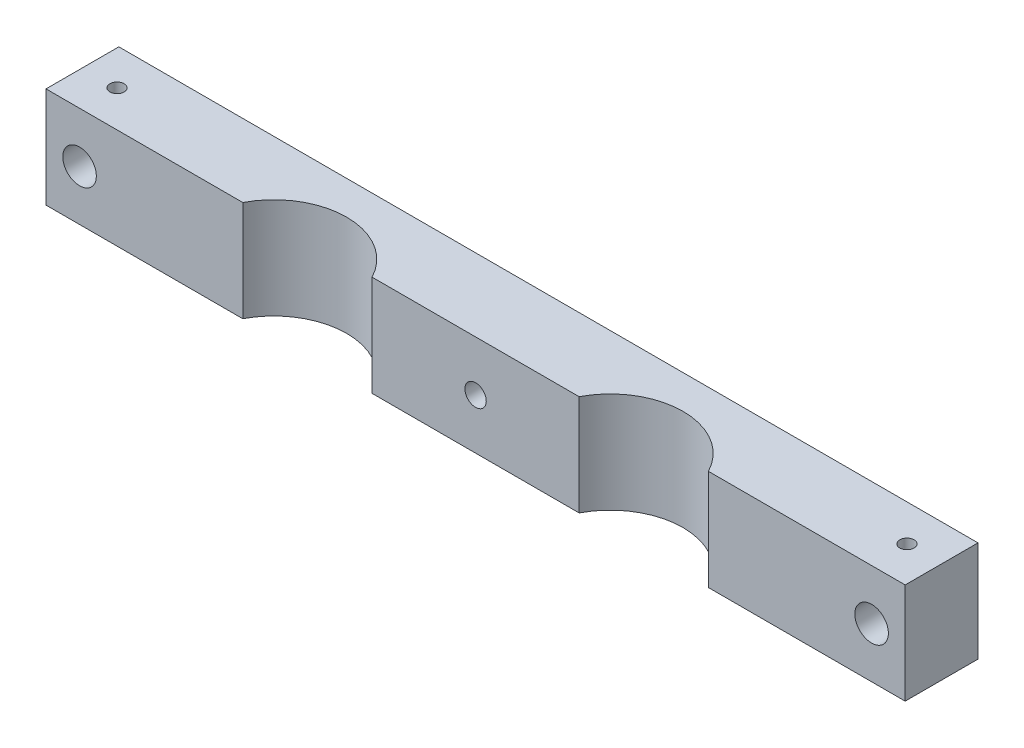
SolidWorks part; units mm, degrees
ref_plane "Front Plane" through (0, 0, 0) normal (0, 0, 1) x (1, 0, 0)
ref_plane "Top Plane" through (0, 0, 0) normal (0, 1, 0) x (1, 0, 0)
ref_plane "Right Plane" through (0, 0, 0) normal (1, 0, 0) x (0, 0, -1)
sketch "Sketch1" plane through (0, 0, 0) normal (0, 1, 0) x (1, 0, 0)
  line L0 (-19.5907, 0) -> (19.5907, 0)
  line L1 (-44.049, 0) -> (44.049, 0) construction
  line L2 (0, 0) -> (0, 13.7795) construction
  line L3 (-81.28, 13.7795) -> (81.28, 13.7795)
  line L4 (81.28, 0) -> (81.28, 13.7795)
  line L5 (44.049, 0) -> (81.28, 0)
  line L6 (-44.049, 0) -> (-81.28, 0)
  line L7 (-81.28, 0) -> (-81.28, 13.7795)
  arc A0 (-19.5907, 0) -> (-44.049, 0) centre (-31.8198, -6.35) ccw
  arc A1 (44.049, 0) -> (19.5907, 0) centre (31.8198, -6.35) ccw
  point P8 (-31.8198, 7.4295)
  dimension "D2" = 13.7795
  dimension "D1" = 162.56
  dimension "D3" = 6.35
  dimension "D4" = 63.6397
  dimension "D5" = 6.35
extrude "Boss-Extrude1" add sketch "Sketch1" along normal blind 19.05
hole_wizard "1/4 (0.25) Diameter Hole1" positions "Sketch3" profile "Sketch2" hole size "1/4" standard "ANSI Inch" end condition through all
sketch "Sketch3" plane through (0, 0, 0) normal (0, 0, 1) x (1, 0, 0)
  line L3 (-44.049, 0) -> (-81.28, 0) construction
  point P0 (-74.93, 9.525)
  dimension "D1" = 74.93
  dimension "D3" = 9.525
sketch "Sketch2" plane through (-74.93, 9.525, 0) normal (1, 0, 0) x (0, -1, 0)
  line L0 (0, 0) -> (0, 13.7795)
  line L1 (0, 13.7795) -> (3.175, 13.7795)
  line L2 (3.175, 13.7795) -> (3.175, 0)
  line L5 (3.175, 0) -> (0, 0)
  line L11 (0, -6.35) -> (0, 107.95) construction
  dimension "Thru Hole Dia." = 6.35
  dimension "Thru Hole Depth" = 13.7795
hole_wizard "#6-32 Tapped Hole1" positions "Sketch5" profile "Sketch4" tap size "#6-32" standard "ANSI Inch"
sketch "Sketch5" plane through (0, 19.05, 0) normal (0, 1, 0) x (1, 0, 0)
  line L0 (-81.28, 0) -> (-81.28, 13.7795) construction
  line L1 (-44.049, 0) -> (-81.28, 0) construction
  point P0 (-74.7293, 6.8897)
  dimension "D1" = 6.5507
  dimension "D2" = 6.8897
sketch "Sketch4" plane through (-74.7293, 19.05, -6.8897) normal (1, 0, 0) x (0, 0, 1)
  line L0 (0, 0) -> (0, 19.05)
  line L1 (0, 19.05) -> (1.3525, 19.05)
  line L2 (1.3525, 19.05) -> (1.3525, 0)
  line L5 (1.3525, 0) -> (0, 0)
  line L11 (0, -6.35) -> (0, 107.95) construction
  dimension "Thru Tap Drill Dia." = 2.7051
  dimension "Thru Tap Drill Depth" = 19.05
cosmetic thread "Hole Thread2" parameters "D2"=3.5052
mirror "Mirror2" about plane through (0, 0, 0) normal (1, 0, 0) of "#6-32 Tapped Hole1", "1/4 (0.25) Diameter Hole1"
hole_wizard "#10-32 Tapped Hole1" positions "Sketch7" profile "Sketch6" tap size "#10-32" standard "ANSI Inch" end condition up to next
sketch "Sketch7" plane through (0, 0, 0) normal (0, 0, 1) x (1, 0, 0)
  circle A0 centre (0, 9.525) radius 2.5527 construction
  circle A1 centre (0, 9.525) radius 2.5527
  point P0 (0, 9.525)
sketch "Sketch6" plane through (0, 9.525, 0) normal (1, 0, 0) x (0, -1, 0)
  line L0 (0, 0) -> (0, 13.7795)
  line L1 (0, 13.7795) -> (2.0193, 13.7795)
  line L2 (2.0193, 13.7795) -> (2.0193, 0)
  line L5 (2.0193, 0) -> (0, 0)
  line L11 (0, -6.35) -> (0, 107.95) construction
  dimension "Thru Tap Drill Dia." = 4.0386
  dimension "Thru Tap Drill Depth" = 13.7795
cosmetic thread "Hole Thread7" parameters "D2"=4.826
